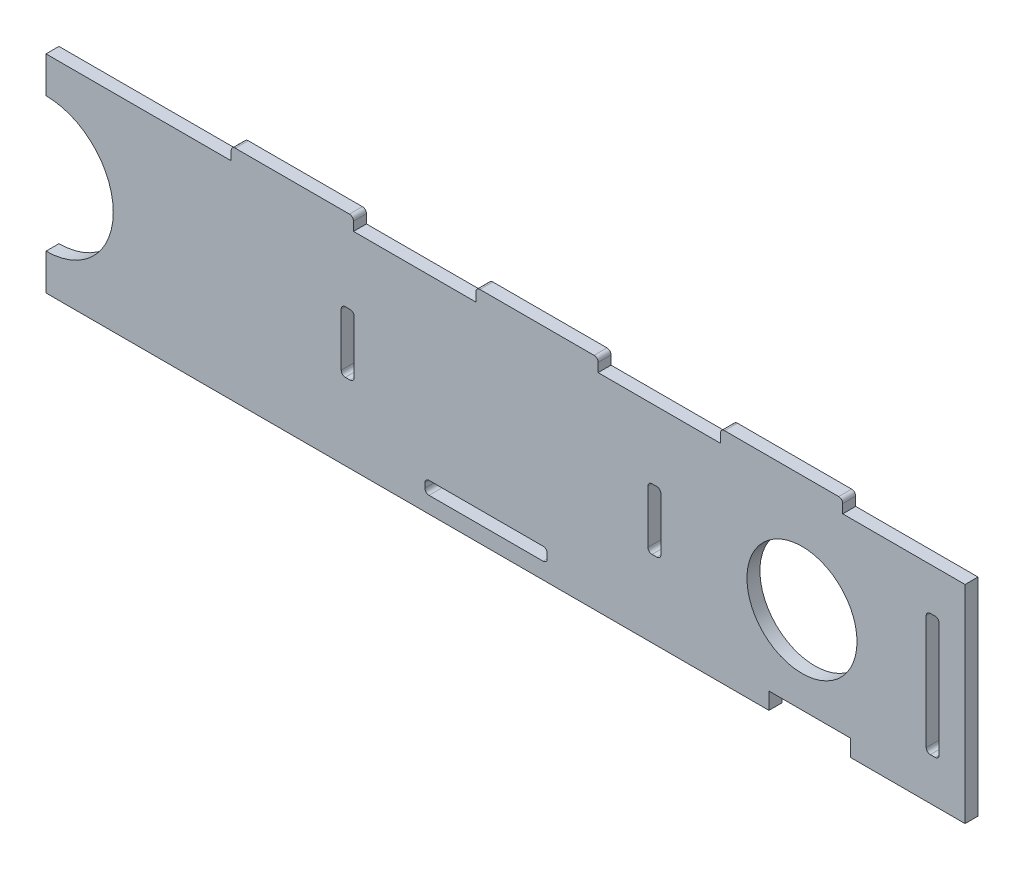
SolidWorks part; units mm, degrees
ref_plane "Front Plane" through (0, 0, 0) normal (0, 0, 1) x (1, 0, 0)
ref_plane "Top Plane" through (0, 0, 0) normal (0, 1, 0) x (1, 0, 0)
ref_plane "Right Plane" through (0, 0, 0) normal (1, 0, 0) x (0, 0, -1)
sketch "Sketch1" plane through (0, 0, 0) normal (0, 0, 1) x (1, 0, 0)
  line L1 (-112.7125, -25.4) -> (112.7125, -25.4)
  line L2 (-112.7125, -25.4) -> (-112.7125, 25.4)
  line L3 (-112.7125, 25.4) -> (112.7125, 25.4)
  line L4 (112.7125, -25.4) -> (112.7125, 25.4)
  line L5 (-112.7125, -25.4) -> (112.7125, 25.4) construction
  line L6 (-112.7125, 25.4) -> (112.7125, -25.4) construction
  point P0 (0, 0)
  dimension "D1" = 225.425
  dimension "D2" = 50.8
extrude "Boss-Extrude1" add sketch "Sketch1" along normal blind 3.175
sketch "Sketch2" plane through (0, 25.4, 0) normal (0, 1, 0) x (1, 0, 0)
  line L0 (112.7125, 0) -> (-112.7125, 0) construction
  line L1 (82.7125, 0) -> (52.7125, 0)
  line L2 (82.7125, 0) -> (82.7125, -3.175)
  line L3 (82.7125, -3.175) -> (52.7125, -3.175)
  line L4 (52.7125, 0) -> (52.7125, -3.175)
  line L5 (112.7125, -3.175) -> (-112.7125, -3.175) construction
  line L6 (112.7125, -3.175) -> (112.7125, 0) construction
  line L7 (22.7125, 0) -> (22.7125, -3.175)
  line L8 (22.7125, 0) -> (-7.2875, 0)
  line L9 (-7.2875, 0) -> (-7.2875, -3.175)
  line L10 (22.7125, -3.175) -> (-7.2875, -3.175)
  line L11 (-37.2875, 0) -> (-37.2875, -3.175)
  line L12 (-37.2875, 0) -> (-67.2875, 0)
  line L13 (-67.2875, 0) -> (-67.2875, -3.175)
  line L14 (-37.2875, -3.175) -> (-67.2875, -3.175)
  point P10 (112.7125, -1.5875)
  dimension "D1" = 30
  dimension "D2" = 30
  dimension "D3" = 3
extrude "Boss-Extrude2" add sketch "Sketch2" along normal blind 3.175
sketch "Sketch3" plane through (0, 0, 3.175) normal (0, 0, 1) x (1, 0, 0)
  line L0 (112.7125, -25.4) -> (112.7125, 25.4) construction
  line L1 (-112.7125, 25.4) -> (-112.7125, -25.4) construction
  circle A0 centre (72.7125, 0) radius 13.5
  circle A1 centre (-112.7125, 0) radius 16.5
  dimension "D2" = 27
  dimension "D3" = 33
  dimension "D1" = 40
extrude "Cut-Extrude1" cut sketch "Sketch3" against normal through all
sketch "Sketch4" plane through (0, 0, 3.175) normal (0, 0, 1) x (1, 0, 0)
  line L0 (106.3625, 25.4) -> (106.3625, -25.4) construction
  line L1 (112.7125, 25.4) -> (82.7125, 25.4) construction
  line L2 (-112.7125, -25.4) -> (112.7125, -25.4) construction
  line L3 (112.7125, -25.4) -> (112.7125, 25.4) construction
  line L4 (106.3625, -15) -> (103.1875, -15)
  line L6 (106.3625, -15) -> (106.3625, 15)
  line L7 (106.3625, 15) -> (103.1875, 15)
  line L8 (103.1875, -15) -> (103.1875, 15)
  dimension "D1" = 6.35
  dimension "D3" = 3.175
extrude "Cut-Extrude2" cut sketch "Sketch4" against normal blind 10
sketch "Sketch5" plane through (0, 0, 3.175) normal (0, 0, 1) x (1, 0, 0)
  line L0 (10.23, -19.8125) -> (112.7125, -19.8125) construction
  line L1 (-112.7125, -25.4) -> (112.7125, -25.4) construction
  line L2 (112.7125, -25.4) -> (112.7125, 25.4) construction
  line L3 (-19.77, -21.4) -> (10.23, -21.4)
  line L4 (-19.77, -21.4) -> (-19.77, -18.225)
  line L5 (-19.77, -18.225) -> (10.23, -18.225)
  line L6 (10.23, -21.4) -> (10.23, -18.225)
  line L7 (-19.77, -21.4) -> (10.23, -18.225) construction
  line L8 (-19.77, -18.225) -> (10.23, -21.4) construction
  dimension "D1" = 3.175
  dimension "D2" = 30
  dimension "D3" = 4
  dimension "D4" = 102.4825
extrude "Cut-Extrude3" cut sketch "Sketch5" against normal through all
sketch "Sketch6" plane through (0, 0, 3.175) normal (0, 0, 1) x (1, 0, 0)
  line L0 (-37.125, -25.4) -> (-37.125, 25.4) construction
  line L1 (-112.7125, -25.4) -> (112.7125, -25.4) construction
  line L2 (-7.2875, 25.4) -> (-37.2875, 25.4) construction
  line L3 (34.925, 25.4) -> (34.925, -25.4) construction
  line L4 (52.7125, 25.4) -> (22.7125, 25.4) construction
  line L7 (36.5125, -6.6) -> (36.5125, -9.6702) construction
  line L12 (-37.125, -6.6) -> (-40.3, -6.6)
  line L13 (-37.125, -6.6) -> (-37.125, 8.4)
  line L14 (-37.125, 8.4) -> (-40.3, 8.4)
  line L15 (-40.3, -6.6) -> (-40.3, 8.4)
  line L16 (34.925, 8.4) -> (38.1, 8.4)
  line L17 (34.925, 8.4) -> (34.925, -6.6)
  line L18 (34.925, -6.6) -> (38.1, -6.6)
  line L19 (38.1, 8.4) -> (38.1, -6.6)
  line L20 (36.5125, -9.6702) -> (112.7125, -9.6702) construction
  line L21 (112.7125, -25.4) -> (112.7125, 25.4) construction
  dimension "D1" = 76.2
  dimension "D2" = 72.05
  dimension "D3" = 15
  dimension "D4" = 3.175
  dimension "D5" = 17
  dimension "D6" = 3.175
extrude "Cut-Extrude4" cut sketch "Sketch6" against normal through all
sketch "Sketch7" plane through (0, 0, 3.175) normal (0, 0, 1) x (1, 0, 0)
  line L0 (-112.7125, -25.4) -> (112.7125, -25.4) construction
  line L1 (64.6125, -25.4) -> (84.6125, -25.4)
  line L2 (64.6125, -25.4) -> (64.6125, -21.2888)
  line L3 (64.6125, -21.2888) -> (84.6125, -21.2888)
  line L4 (84.6125, -25.4) -> (84.6125, -21.2888)
  line L5 (112.7125, -25.4) -> (112.7125, 25.4) construction
  dimension "D1" = 20
  dimension "D2" = 28.1
extrude "Cut-Extrude5" cut sketch "Sketch7" against normal through all
fillet "Fillet1" radius 1 22 edges at (-37.125, -6.6, 1.5875) (-40.3, -6.6, 1.5875) (-37.125, 8.4, 1.5875) (-40.3, 8.4, 1.5875) (-19.77, -18.225, 1.5875) (-19.77, -21.4, 1.5875) (10.23, -18.225, 1.5875) (10.23, -21.4, 1.5875) (38.1, -6.6, 1.5875) (34.925, -6.6, 1.5875) (38.1, 8.4, 1.5875) (34.925, 8.4, 1.5875) (103.1875, 15, 1.5875) (106.3625, 15, 1.5875) (103.1875, -15, 1.5875) (106.3625, -15, 1.5875) (82.7125, 28.575, 1.5875) (52.7125, 28.575, 1.5875) (-7.2875, 28.575, 1.5875) (22.7125, 28.575, 1.5875) (-37.2875, 28.575, 1.5875) (-67.2875, 28.575, 1.5875)
